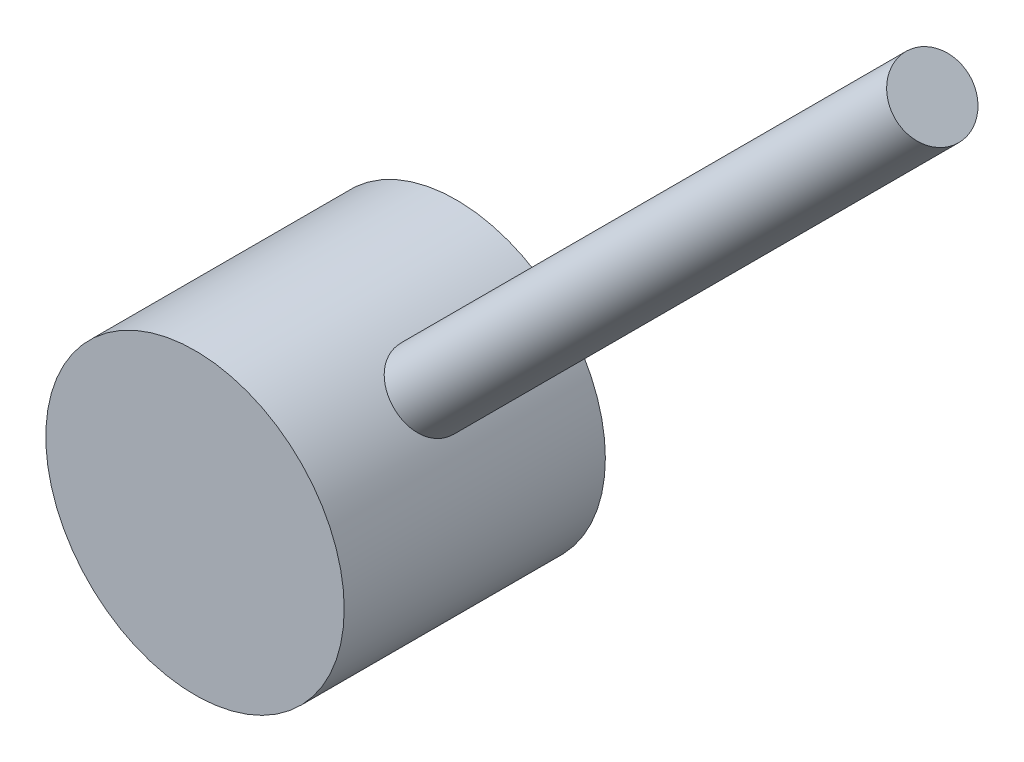
SolidWorks part; units mm, degrees
ref_plane "Front Plane" through (0, 0, 0) normal (0, 0, 1) x (1, 0, 0)
ref_plane "Top Plane" through (0, 0, 0) normal (0, 1, 0) x (1, 0, 0)
ref_plane "Right Plane" through (0, 0, 0) normal (1, 0, 0) x (0, 0, -1)
sketch "Sketch1" plane through (0, 0, 0) normal (0, 0, 1) x (1, 0, 0)
  circle A0 centre (0, 0) radius 4
  dimension "D1" = 8
extrude "Cylinder on Wire end" add sketch "Sketch1" along normal blind 4.5 and the other way blind 2.5
ref_plane "Plane1" through (2.8284, 2.8284, 0) normal (0.7071, 0.7071, 0) x (0.7071, -0.7071, 0)
ref_plane "Plane2" through (-1.4142, -1.4142, 0) normal (0.7071, 0.7071, 0) x (0.7071, -0.7071, 0)
sketch "Sketch4" plane through (-1.4142, -1.4142, 0) normal (0.7071, 0.7071, 0) x (0.7071, -0.7071, 0)
  line L0 (4, 2.5) -> (-4, 2.5) construction
  circle A0 centre (0, -1) radius 1
  dimension "D2" = 2
  dimension "D1" = 3.5
extrude "Wire" add sketch "Sketch4" along normal blind 25
